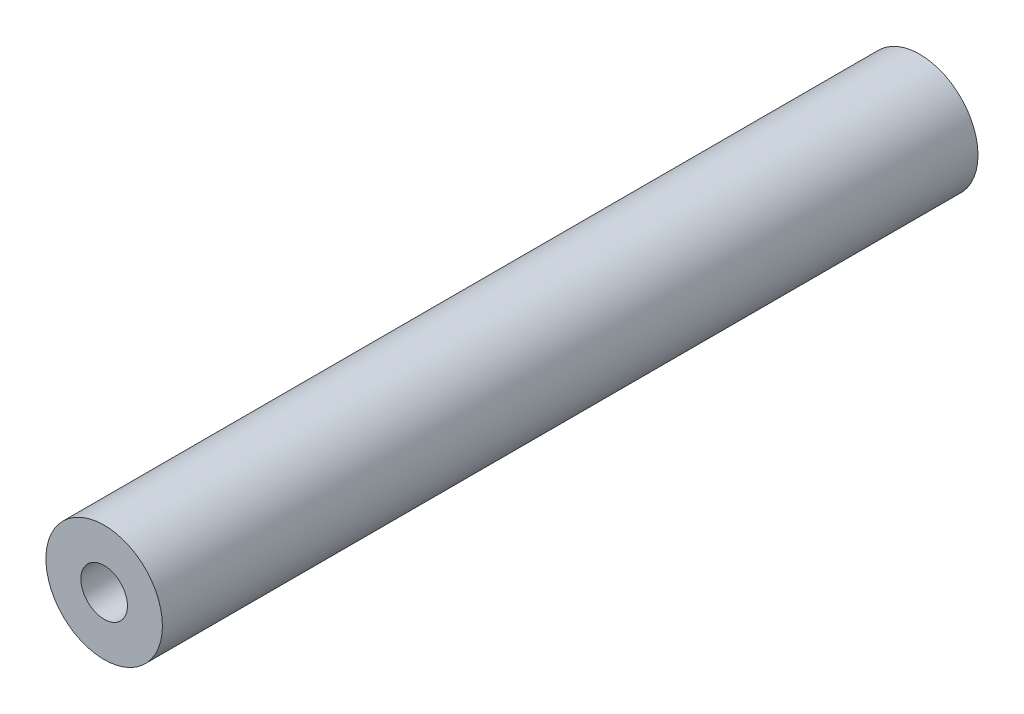
SolidWorks part; units mm, degrees
material "ABS"
ref_plane "Front Plane" through (0, 0, 0) normal (0, 0, 1) x (1, 0, 0)
ref_plane "Top Plane" through (0, 0, 0) normal (0, 1, 0) x (1, 0, 0)
ref_plane "Right Plane" through (0, 0, 0) normal (1, 0, 0) x (0, 0, -1)
sketch "Sketch1" plane through (0, 0, 0) normal (0, 0, 1) x (1, 0, 0)
  circle A0 centre (0, 0) radius 5
  circle A1 centre (0, 0) radius 2
  dimension "D1" = 10
  dimension "D2" = 4
extrude "Boss-Extrude1" add sketch "Sketch1" along normal blind 70
